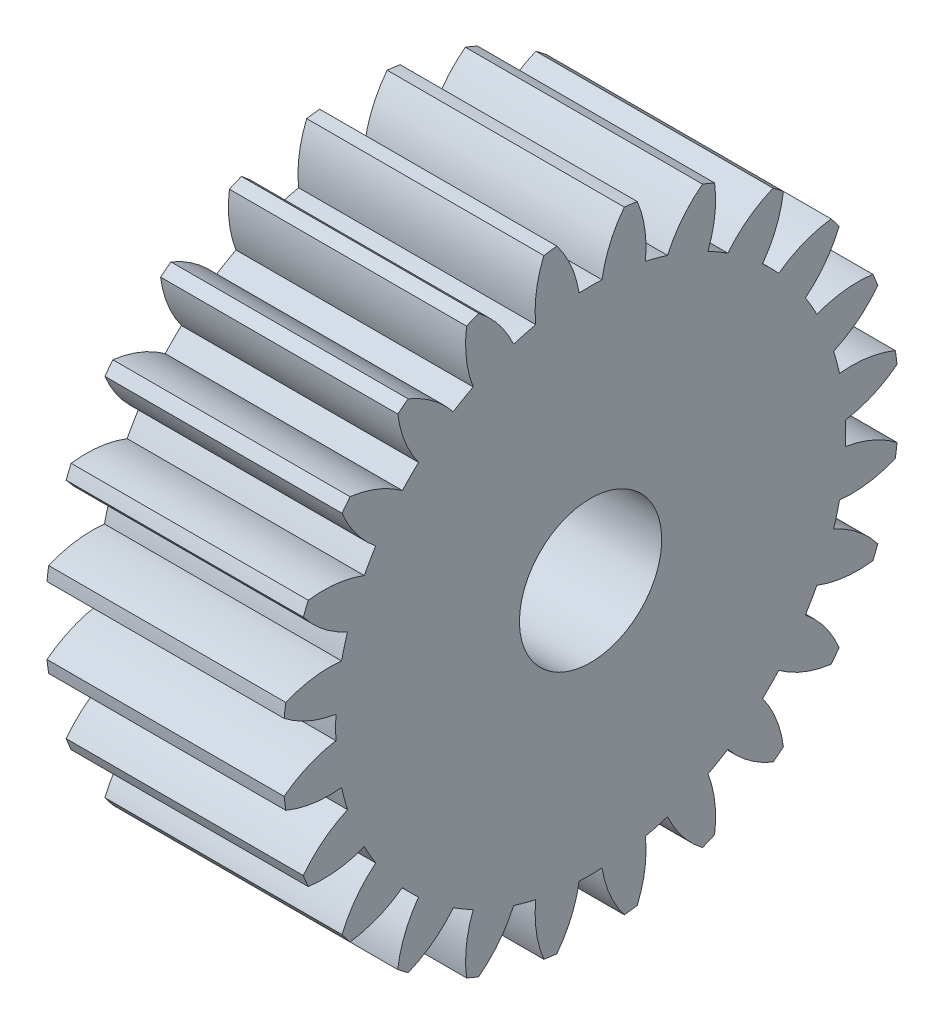
SolidWorks part; units mm, degrees
ref_plane "Plane1" through (0, 0, 0) normal (0, 0, 1) x (1, 0, 0)
ref_plane "Plane2" through (0, 0, 0) normal (0, 1, 0) x (1, 0, 0)
ref_plane "Plane3" through (0, 0, 0) normal (1, 0, 0) x (0, 0, -1)
other "Configuration Table"
sketch "HoldingSke" plane through (0, 0, 0) normal (0, 1, 0) x (1, 0, 0)
  line L0 (0, 0) -> (0.9135, -0.4067)
  line L1 (-15, 0) -> (100, 0) construction
  line L2 (0, 0) -> (-2.1039, 2.3779)
  line L3 (0, 0) -> (-11.863, 4.5341)
  line L4 (0, 0) -> (7.8894, 3.5126)
  line L5 (0, 0) -> (-46.8476, -17.4728)
  line L6 (0, 0) -> (-8.2896, -5.593)
  line L7 (-2.1039, 2.3779) -> (8.6586, 51.2059)
  line L8 (-76.2, 54.61) -> (-75.2, 54.61)
  line L9 (-71.009, 38.7566) -> (-53.1078, 45.2721)
  line L10 (-76.2, 71.12) -> (104.1128, 71.12)
  line L11 (0, 0) -> (-10, 0)
  line L12 (-76.2, 101.6) -> (-76.162, 101.6)
  line L13 (24.9733, 27.94) -> (52.9518, 28.4284)
  line L14 (24.9733, 27.94) -> (24.9743, 27.94)
  line L15 (24.9733, 27.94) -> (100.4006, 29.5858)
  line L16 (-63.627, -1) -> (-12.827, -1)
  circle A0 centre (0, 0) radius 3
  circle A1 centre (0, 0) radius 10.749
  circle A2 centre (0, 0) radius 37.5
  circle A3 centre (0, 0) radius 3
  dimension "MHD" = 21.498
  dimension "Hub_dia" = 75
  dimension "Bore" = 6
  dimension "MBD" = 6
  dimension "Num_teeth" = 24
  dimension "Pitch" = 1
  dimension "Overall_len" = 50
  dimension "Show_teeth" = 24
  dimension "Thickness" = 10
  dimension "OAL" = 50.0001
  dimension "T_dim" = 1
  dimension "Ap" = 20
  dimension "H" = 19.05
  dimension "Pitch_radius" = 180.3128
  dimension "Width" = 10
  dimension "Backlash" = 0.038
  dimension "Addendum_fac" = 1
  dimension "Dedendum_fac" = 1.25
  dimension "Clearance_fac" = 0.25
  dimension "Dedendum_add" = 0.001
  dimension "Module" = 1
sketch "BasProSke" plane through (0, 0, 0) normal (0, 1, 0) x (1, 0, 0)
  line L0 (-10, 0) -> (60, 0) construction
  line L1 (0, 0) -> (0, 13)
  line L2 (0, 0) -> (10, 0)
  line L3 (10, 0) -> (10, 13)
  line L4 (10, 13) -> (0, 13)
  dimension "Thickness" = 10
  dimension "Diameter" = 26
revolve "Base-Revolve" add sketch "BasProSke" angle 360 about L0
sketch "TooCutSke" plane through (0, 0, 0) normal (1, 0, 0) x (0, 0, -1)
  line L1 (0, 0) -> (0, 107) construction
  line L2 (0, 0) -> (-0.8513, 11.9698) construction
  line L3 (0, 0) -> (-3.127, 23.752) construction
  line L4 (-0.8513, 11.9698) -> (-1.5635, 11.876) construction
  arc A0 (0.4834, 10.7381) -> (-0.4834, 10.7381) centre (0, 0) ccw
  arc A1 (1.4409, 12.9455) -> (-1.4409, 12.9455) centre (0, 0) ccw
  circle A2 centre (0, 0) radius 12 construction
  circle A3 centre (0, 0) radius 11.2763 construction
  arc A4 (-0.4834, 10.7381) -> (-1.4409, 12.9455) centre (-5.2252, 9.9926) ccw
  arc A5 (1.4409, 12.9455) -> (0.4834, 10.7381) centre (5.2252, 9.9926) ccw
  dimension "Root_dia" = 21.498
  dimension "Overcut_dia" = 26.0508
  dimension "Pitch_dia" = 24
  dimension "Base_dia" = 22.5526
  dimension "Flank_rad" = 4.8
  dimension "Half_ang" = 7.5
  dimension "Half_CT" = 0.7183
extrude "ToothCut" cut sketch "TooCutSke" along normal through all
fillet "Breaks" [suppressed] radius 0.02
fillet "RootFillets" [suppressed] radius 0.251
pattern_circular "TeethCuts" count 24 every 15 about axis through (-10, 0, 0) along (1, 0, 0) of "ToothCut", "RootFillets", "Breaks"
sketch "HubNeaOneSke" plane through (0, 0, 0) normal (-1, 0, 0) x (0, 0, 1)
  circle A0 centre (0, 0) radius 10.749
  dimension "Diameter" = 21.498
extrude "HubNearOne" [suppressed] add sketch "HubNeaOneSke" along normal blind 40.0001
sketch "HubNeaBotSke" plane through (0, 0, 0) normal (-1, 0, 0) x (0, 0, 1)
  circle A0 centre (0, 0) radius 10.749
  dimension "Diameter" = 21.498
extrude "HubNearBoth" [suppressed] add sketch "HubNeaBotSke" along normal blind 20
ref_plane "FarPln" through (10, 0, 0) normal (1, 0, 0) x (0, 0, -1)
sketch "HubFarSke" plane through (10, 0, 0) normal (1, 0, 0) x (0, 0, -1)
  circle A0 centre (0, 0) radius 10.749
  dimension "Diameter" = 21.498
extrude "HubFar" [suppressed] add sketch "HubFarSke" along normal blind 20
sketch "BorSke" plane through (0, 0, 0) normal (1, 0, 0) x (0, 0, -1)
  circle A0 centre (0, 0) radius 3
  dimension "Diameter" = 6
extrude "Bore" cut sketch "BorSke" along normal mid plane 100.0001
sketch "KeySke" plane through (0, 0, 0) normal (1, 0, 0) x (0, 0, -1)
  line L0 (-1, 0) -> (-1, 4)
  line L1 (-1, 4) -> (1, 4)
  line L2 (1, 4) -> (1, 0)
  line L3 (0, 0) -> (0, 34) construction
  line L4 (-1, 0) -> (1, 0)
  dimension "Offset" = 4
  dimension "Width" = 2
extrude "Keyway" [suppressed] cut sketch "KeySke" along normal mid plane 100.0001
pattern_circular "Keyway2" [suppressed] count 2 every 90 about axis through (-10, 0, 0) along (1, 0, 0)
equation "' \"Module@HoldingSke\" = 6.35"
equation "' \"Num_teeth@HoldingSke\" = 12"
equation "' \"Ap@HoldingSke\" =  20"
equation "' \"Ap@HoldingSke\" = 20"
equation "' \"Width@HoldingSke\" = 0.5 * 25.4"
equation "' \"Hub_dia@HoldingSke\"= 1 * 25.4"
equation "' \"Hub_dia@HoldingSke\" = 1 * 25.4"
equation "' \"Overall_len@HoldingSke\" = 1.0 * 25.4"
equation "' \"Bore@HoldingSke\" = 0.75 * 25.4"
equation "' \"T_dim@HoldingSke\" = 0.1 * 25.4"
equation "' \"Width@KeySke\" = 0.25 * 25.4"
equation "' \"Show_teeth@HoldingSke\" = 13"
equation "' \"Backlash@HoldingSke\" = 0.009 * 25.4"
equation "' \"Addendum_fac@HoldingSke\" = 1.0"
equation "' \"Dedendum_fac@HoldingSke\" = 1.25"
equation "' \"Dedendum_add@HoldingSke\" = 0.00005 * 25.4"
equation "' \"Clearance_fac@HoldingSke\" = 0.25"
equation "\"Pitch@HoldingSke\" = 1 / \"Module@HoldingSke\""
equation "\"Overcut_dia@TooCutSke\" = (\"Num_teeth@HoldingSke\" + 2 * \"Addendum_fac@HoldingSke\") / \"Pitch@HoldingSke\" + 0.002 * 25.4"
equation "\"Pitch_dia@TooCutSke\" = \"Num_teeth@HoldingSke\" / \"Pitch@HoldingSke\""
equation "\"Base_dia@TooCutSke\" = \"Num_teeth@HoldingSke\" / \"Pitch@HoldingSke\" * cos((\"Ap@HoldingSke\"  * 3.14159265 / 180))"
equation "\"Root_dia@TooCutSke\" = (\"Num_teeth@HoldingSke\" + 2) / \"Pitch@HoldingSke\" - 2 * (\"Addendum_fac@HoldingSke\" + \"Dedendum_fac@HoldingSke\") / \"Pitch@HoldingSke\" - \"Dedendum_add@HoldingSke\" * 2"
equation "\"Half_ang@TooCutSke\" = 180 / \"Num_teeth@HoldingSke\""
equation "\"Half_CT@TooCutSke\" = \"Num_teeth@HoldingSke\" / \"Pitch@HoldingSke\" * sin((3.14159265 / 2 / \"Num_teeth@HoldingSke\")) / 2 - 7 * \"Backlash@HoldingSke\" / 4"
equation "\"Flank_rad@TooCutSke\" = \"Num_teeth@HoldingSke\" / \"Pitch@HoldingSke\" / 5"
equation "\"Radius@RootFillets\" = \"Clearance_fac@HoldingSke\" / \"Pitch@HoldingSke\" + \"Dedendum_add@HoldingSke\""
equation "\"Break_rad@Breaks\" = 0.02 / \"Pitch@HoldingSke\""
equation "\"Thickness@HoldingSke\" = \"Width@HoldingSke\""
equation "\"OAL@HoldingSke\" = \"Thickness@HoldingSke\""
equation "\"MHD@HoldingSke\" = (\"Num_teeth@HoldingSke\" + 2) / \"Pitch@HoldingSke\" - 2 * (\"Addendum_fac@HoldingSke\" + \"Dedendum_fac@HoldingSke\")  / \"Pitch@HoldingSke\" - \"Dedendum_add@HoldingSke\" * 2"
equation "\"MBD@HoldingSke\" = (\"Num_teeth@HoldingSke\" + 2) / \"Pitch@HoldingSke\" - 2 * (\"Addendum_fac@HoldingSke\" + \"Dedendum_fac@HoldingSke\")  / \"Pitch@HoldingSke\" - \"Dedendum_add@HoldingSke\" * 2 - 0.002 * 25.4"
equation "\"MHD@HoldingSke\" = ((sgn( \"MHD@HoldingSke\" - \"Hub_dia@HoldingSke\" )-1)*( \"MHD@HoldingSke\" - \"Hub_dia@HoldingSke\" ))/-2+ \"Hub_dia@HoldingSke\""
equation "\"MBD@HoldingSke\" = ((sgn( \"MBD@HoldingSke\" - \"Bore@HoldingSke\" )-1)*( \"MBD@HoldingSke\" - \"Bore@HoldingSke\" ))/-2+ \"Bore@HoldingSke\""
equation "\"OAL@HoldingSke\" = ((sgn( \"OAL@HoldingSke\" - \"Overall_len@HoldingSke\" )+1)*( \"OAL@HoldingSke\" - \"Overall_len@HoldingSke\" ))/2 + \"Overall_len@HoldingSke\" + 0.000002 * 25.4"
equation "\"Num_teeth@TeethCuts\" = int( \"Show_teeth@HoldingSke\" ) + 1"
equation "\"Num_teeth@TeethCuts\" = ((sgn( \"Num_teeth@TeethCuts\" - \"Num_teeth@HoldingSke\" )-1)*( \"Num_teeth@TeethCuts\" - \"Num_teeth@HoldingSke\" ))/-2+ \"Num_teeth@HoldingSke\""
equation "\"Num_teeth@TeethCuts\" = ((sgn( \"Num_teeth@TeethCuts\" - 2.0)+1)*( \"Num_teeth@TeethCuts\" - 2.0))/2 +2.0"
equation "\"Angle@TeethCuts\" = 360.0 / \"Num_teeth@HoldingSke\""
equation "\"Diameter@BasProSke\" = (\"Num_teeth@HoldingSke\" + 2 * \"Addendum_fac@HoldingSke\") / \"Pitch@HoldingSke\""
equation "\"Thickness@BasProSke\"  = \"Thickness@HoldingSke\""
equation "' \"Fillet_rad@BasProSke\" =  \"Thickness@HoldingSke\" * 0.05"
equation "' \"Fillet_rad@BasProSke\" = \"Thickness@HoldingSke\" * 0.05"
equation "\"MHD@HoldingSke\" = ((sgn( \"MHD@HoldingSke\" - \"Root_dia@TooCutSke\" )-1)*( \"MHD@HoldingSke\" - \"Root_dia@TooCutSke\" ))/-2+ \"Root_dia@TooCutSke\""
equation "\"Diameter@HubNeaOneSke\" = \"MHD@HoldingSke\""
equation "\"Length@HubNearOne\" = \"OAL@HoldingSke\" - \"Thickness@BasProSke\""
equation "\"Diameter@HubNeaBotSke\" = \"MHD@HoldingSke\""
equation "\"Length@HubNearBoth\" = ( \"OAL@HoldingSke\" - \"Thickness@BasProSke\" ) / 2.0"
equation "\"Thickness@FarPln\" = \"Thickness@BasProSke\""
equation "\"Diameter@HubFarSke\" = \"MHD@HoldingSke\""
equation "\"Length@HubFar\" = ( \"OAL@HoldingSke\" - \"Thickness@BasProSke\" ) / 2.0"
equation "\"Diameter@BorSke\" = \"MBD@HoldingSke\""
equation "\"D1@Bore\" = \"OAL@HoldingSke\" * 2.0"
equation "\"D1@Keyway\" = \"OAL@HoldingSke\" * 2.0"
equation "\"Offset@KeySke\" = \"T_dim@HoldingSke\" + \"MBD@HoldingSke\" / 2.0"
